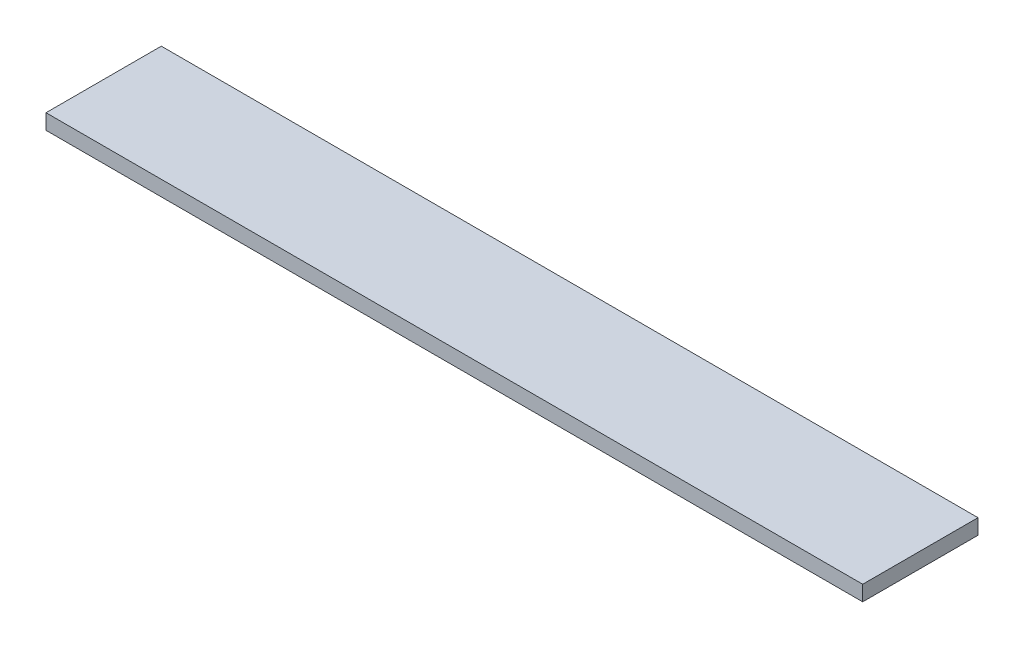
SolidWorks part; units mm, degrees
ref_plane "Front Plane" through (0, 0, 0) normal (0, 0, 1) x (1, 0, 0)
ref_plane "Top Plane" through (0, 0, 0) normal (0, 1, 0) x (1, 0, 0)
ref_plane "Right Plane" through (0, 0, 0) normal (1, 0, 0) x (0, 0, -1)
sketch "Sketch1" plane through (0, 0, 0) normal (0, 1, 0) x (1, 0, 0)
  line L1 (-42.5, -6) -> (42.5, -6)
  line L2 (-42.5, -6) -> (-42.5, 6)
  line L3 (-42.5, 6) -> (42.5, 6)
  line L4 (42.5, -6) -> (42.5, 6)
  line L5 (-42.5, -6) -> (42.5, 6) construction
  line L6 (-42.5, 6) -> (42.5, -6) construction
  point P0 (0, 0)
  dimension "D1" = 85
  dimension "D2" = 12
extrude "Boss-Extrude1" add sketch "Sketch1" along normal blind 1.5875
